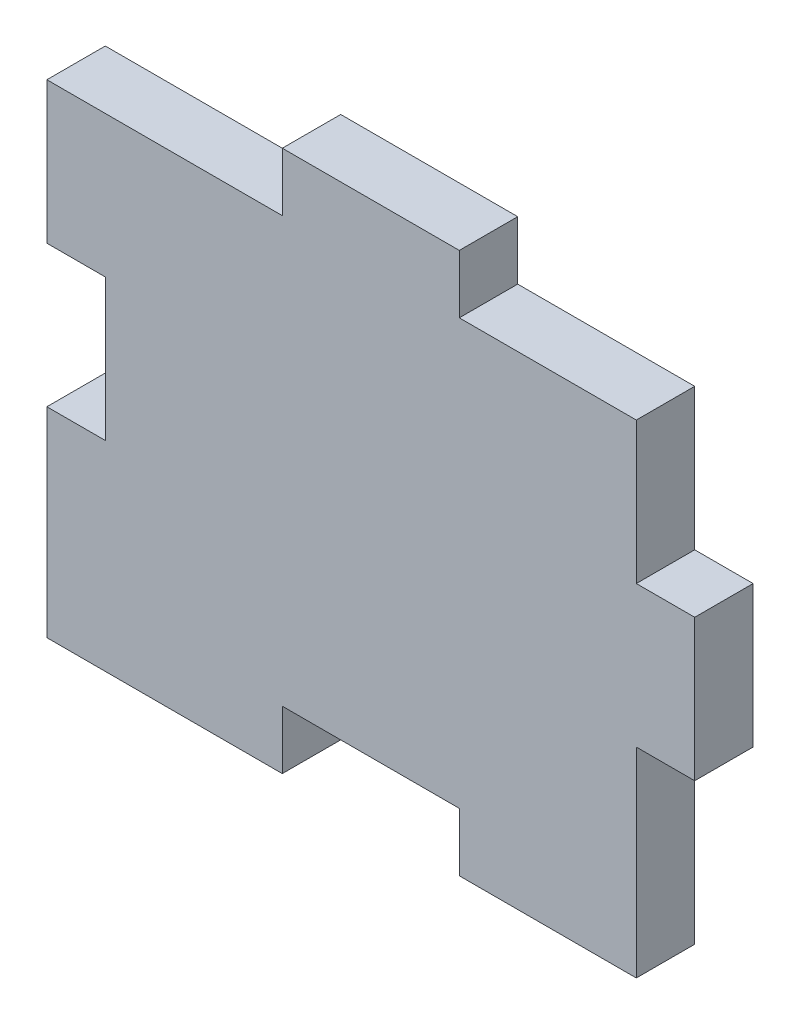
SolidWorks part; units mm, degrees
ref_plane "Front Plane" through (0, 0, 0) normal (0, 0, 1) x (1, 0, 0)
ref_plane "Top Plane" through (0, 0, 0) normal (0, 1, 0) x (1, 0, 0)
ref_plane "Right Plane" through (0, 0, 0) normal (1, 0, 0) x (0, 0, -1)
sketch "Sketch1" plane through (0, 0, 0) normal (0, 0, 1) x (1, 0, 0)
  line L1 (16.6667, 0) -> (33.3333, 0)
  line L3 (0, 40) -> (16.6667, 40)
  line L4 (50, 0) -> (50, 13.3333)
  line L5 (50, 26.6667) -> (50, 40)
  line L7 (0, -5.5) -> (16.6667, -5.5)
  line L8 (16.6667, 0) -> (16.6667, -5.5)
  line L9 (33.3333, 40) -> (50, 40)
  line L10 (50, 0) -> (50, -5.5)
  line L11 (50, -5.5) -> (33.3333, -5.5)
  line L12 (33.3333, 0) -> (33.3333, -5.5)
  line L13 (50, 26.6667) -> (55.5, 26.6667)
  line L14 (0, 26.6667) -> (0, 13.3333)
  line L15 (50, 13.3333) -> (55.5, 13.3333)
  line L16 (55.5, 26.6667) -> (55.5, 13.3333)
  line L18 (0, 40) -> (-5.5, 40)
  line L22 (16.6667, 40) -> (16.6667, 45.5)
  line L23 (16.6667, 45.5) -> (33.3333, 45.5)
  line L24 (33.3333, 40) -> (33.3333, 45.5)
  line L25 (0, 26.6667) -> (-5.5, 26.6667)
  line L26 (-5.5, 40) -> (-5.5, 26.6667)
  line L27 (0, 13.3333) -> (-5.5, 13.3333)
  line L29 (0, -5.5) -> (-5.5, -5.5)
  line L30 (-5.5, 13.3333) -> (-5.5, -5.5)
  dimension "D1" = 50
  dimension "D2" = 40
  dimension "D3" = 0
  dimension "D4" = 5.5
extrude "Boss-Extrude1" add sketch "Sketch1" along normal blind 5.5
equation "\"mat\"=\"mat@hobby motor air spinner.assembly\""
equation "\"D4@Sketch1\" = \"mat\""
equation "\"D1@Boss-Extrude1\"=\"mat\""
